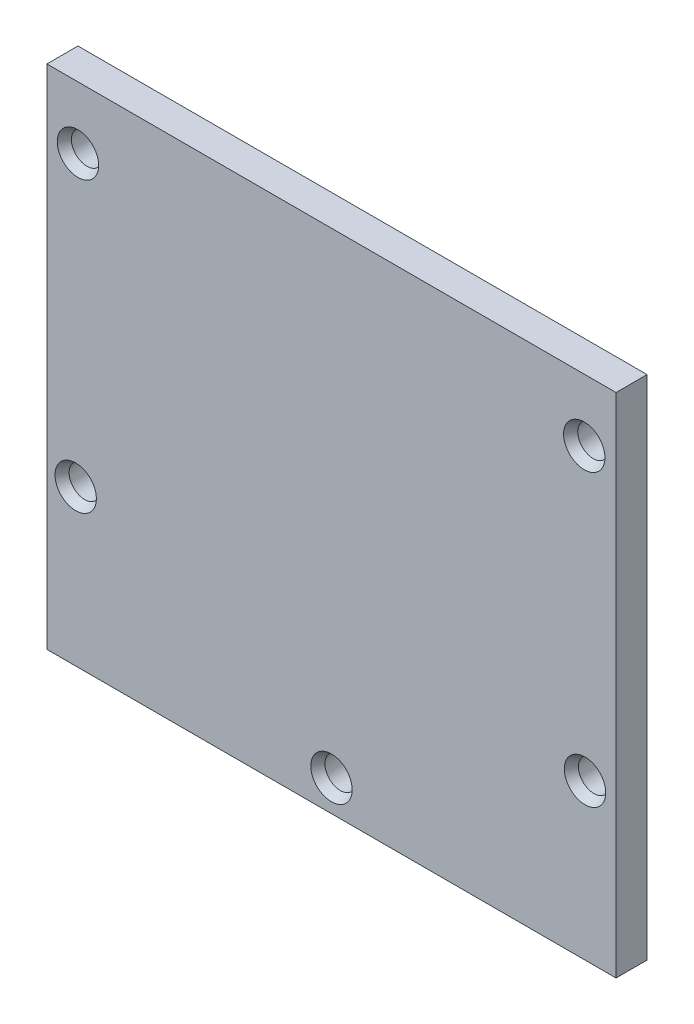
SolidWorks part; units mm, degrees
ref_plane "Front" through (0, 0, 0) normal (0, 0, 1) x (1, 0, 0)
ref_plane "Top" through (0, 0, 0) normal (0, 1, 0) x (1, 0, 0)
ref_plane "Right" through (0, 0, 0) normal (1, 0, 0) x (0, 0, -1)
sketch "Эскиз1" plane through (0, 0, 0) normal (0, 0, 1) x (1, 0, 0)
  line L1 (-27.5, -27.5) -> (27.5, -27.5)
  line L2 (-27.5, -27.5) -> (-27.5, 21.5)
  line L3 (-27.5, 21.5) -> (27.5, 21.5)
  line L4 (27.5, -27.5) -> (27.5, 21.5)
  circle A0 centre (-24.5, 15.5) radius 1.5
  circle A1 centre (-24.7187, -12.5) radius 1.5
  circle A2 centre (24.5, -12.5) radius 1.5
  circle A3 centre (24.4304, 15.5) radius 1.5
  circle A4 centre (0, -24.5) radius 1.5
  dimension "D1" = 3
  dimension "D2" = 3
  dimension "D3" = 3
  dimension "D4" = 3
  dimension "D5" = 6
  dimension "D6" = 15
extrude "Бобышка-Вытянуть1" add sketch "Эскиз1" along normal blind 3
chamfer "Фаска1" distance 0.5 angle 60 5 edges at (-23, 15.5, 3) (26, -12.5, 3) (25.9304, 15.5, 3) (-23.2187, -12.5, 3) (1.5, -24.5, 3)
